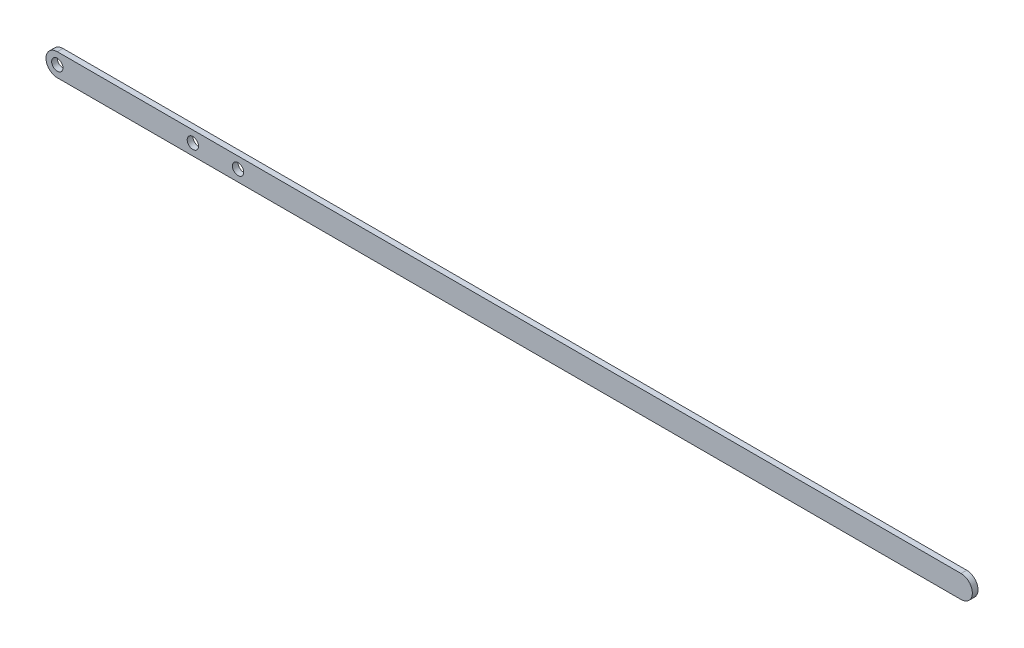
SolidWorks part; units mm, degrees
ref_plane "Front Plane" through (0, 0, 0) normal (0, 0, 1) x (1, 0, 0)
ref_plane "Top Plane" through (0, 0, 0) normal (0, 1, 0) x (1, 0, 0)
ref_plane "Right Plane" through (0, 0, 0) normal (1, 0, 0) x (0, 0, -1)
sketch "Sketch1" plane through (0, 0, 0) normal (0, 0, 1) x (1, 0, 0)
  line L0 (-254, 0) -> (254, 0) construction
  line L1 (-254, 6.35) -> (254, 6.35)
  line L2 (-254, -6.35) -> (254, -6.35)
  arc A0 (-254, 6.35) -> (-254, -6.35) centre (-254, 0) ccw
  arc A1 (254, -6.35) -> (254, 6.35) centre (254, 0) ccw
  circle A2 centre (-254, 0) radius 3.175
  circle A3 centre (-177.8, 0) radius 3.175
  circle A4 centre (-152.4, 0) radius 3.175
  point P2 (0, 0)
  dimension "D3" = 6.35
  dimension "D1" = 12.7
  dimension "D2" = 508
  dimension "D4" = 76.2
  dimension "D5" = 25.4
extrude "Boss-Extrude2" add sketch "Sketch1" along normal blind 3.175
